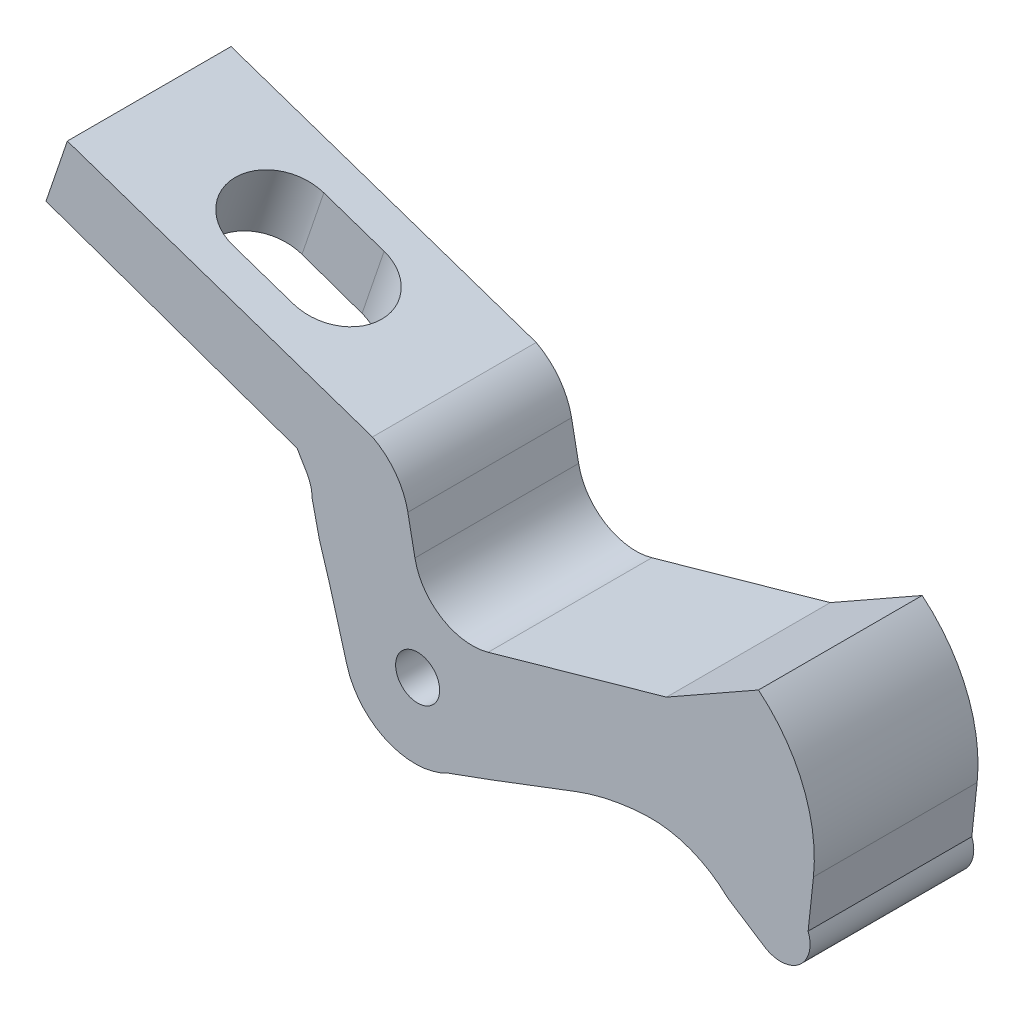
SolidWorks part; units mm, degrees
ref_plane "Plan de face" through (0, 0, 0) normal (0, 0, 1) x (1, 0, 0)
ref_plane "Plan de dessus" through (0, 0, 0) normal (0, 1, 0) x (1, 0, 0)
ref_plane "Plan de droite" through (0, 0, 0) normal (1, 0, 0) x (0, 0, -1)
sketch "Esquisse1" plane through (0, 0, 0) normal (0, 0, 1) x (1, 0, 0)
  line L0 (-1012.8934, -243.5975) -> (352.4399, -243.5975) construction
  line L1 (4.7658, 46.8225) -> (88.393, 17.5572) construction
  line L2 (7.3094, 53.7143) -> (40.8576, 42.3111)
  line L3 (7.3094, 53.7143) -> (4.9633, 46.8122)
  line L4 (4.9633, 46.8122) -> (32.5713, 37.0877)
  line L5 (32.5713, 37.0877) -> (33.6103, 35.3392)
  line L6 (34.2323, 33.1217) -> (35.0165, 29.6331)
  line L7 (35.0165, 29.6331) -> (36.0982, 26.1175)
  line L8 (36.0982, 26.1175) -> (38.0506, 19.1999)
  line L9 (49.1997, 14.4668) -> (53.8801, 16.1762)
  line L10 (53.8801, 16.1762) -> (63.1672, 19.7061)
  line L11 (79.9223, 17.9411) -> (83.9677, 15.3215)
  line L12 (88.7584, 19.1999) -> (89.3439, 24.6514)
  line L13 (83.3016, 39.4398) -> (77.6866, 36.2554)
  line L14 (77.6866, 36.2554) -> (73.1896, 33.7051)
  line L15 (73.1896, 33.7051) -> (60.3349, 30.0771)
  line L16 (60.3349, 30.0771) -> (53.5789, 28.1703)
  line L17 (45.5254, 33.1217) -> (44.7493, 37.0877)
  line L18 (4.9633, 46.8122) -> (4.9633, 37.0877) construction
  line L19 (88.7584, 19.1999) -> (88.7584, 5.4646) construction
  arc A0 (33.6103, 35.3392) -> (34.2323, 33.1217) centre (29.7982, 33.074) cw
  arc A1 (38.0506, 19.1999) -> (49.1997, 14.4668) centre (45.5254, 21.3095) ccw
  arc A2 (63.1672, 19.7061) -> (71.0329, 21.3095) centre (72.0013, -3.5359) cw
  arc A3 (71.0329, 21.3095) -> (79.9223, 17.9411) centre (71.507, 9.1466) cw
  arc A4 (83.9677, 15.3215) -> (88.7584, 19.1999) centre (85.7299, 18.0428) ccw
  arc A5 (89.3439, 24.6514) -> (83.3016, 39.4398) centre (72.6215, 26.4475) ccw
  arc A6 (53.5789, 28.1703) -> (45.5254, 33.1217) centre (51.8331, 34.356) cw
  arc A7 (44.7493, 37.0877) -> (40.8576, 42.3111) centre (37.3563, 35.641) ccw
  circle A8 centre (45.8228, 21.8786) radius 2.4205
  dimension "D1" = 88.6
  dimension "D2" = 83.795
extrude "Boss.-Extru.1" add sketch "Esquisse1" along normal blind 18 contours L7 L8 A1 L9 L10 A2 A3 L11 A4 L12 A5 L13 L14 L15 L16 A6 L17 A7 L2 L3 L4 L5 A0 L6 | A8
sketch "Esquisse2" plane through (17.124, 50.3783, 0) normal (0.3218, 0.9468, 0) x (0.9468, -0.3218, 0)
  line L0 (4.634, -14) -> (11.634, -14)
  line L1 (11.634, -4) -> (4.634, -4)
  line L2 (-0.366, -9) -> (-0.366, -2.7006) construction
  line L3 (16.634, -9) -> (16.634, -1.3457) construction
  line L4 (-10.366, -18) -> (-10.366, 0) construction
  line L5 (-0.366, -9) -> (-5.6843, -9) construction
  line L6 (-10.366, -9) -> (-8.2899, -9) construction
  arc A0 (11.634, -14) -> (11.634, -4) centre (11.634, -9) ccw
  arc A1 (4.634, -4) -> (4.634, -14) centre (4.634, -9) ccw
  dimension "D1" = 17
  dimension "D2" = 10
  dimension "D3" = 10
extrude "Enlèv. mat.-Extru.1" cut sketch "Esquisse2" against normal through all
